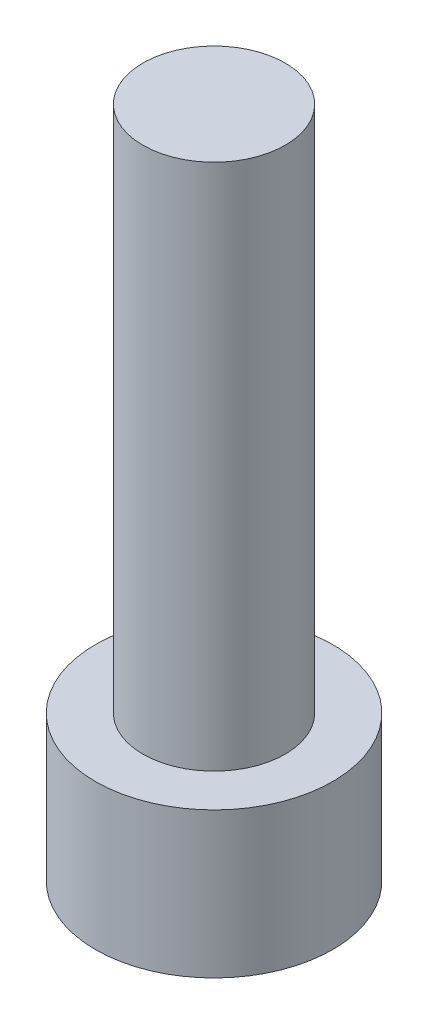
SolidWorks part; units mm, degrees
ref_plane "Front Plane" through (0, 0, 0) normal (0, 0, 1) x (1, 0, 0)
ref_plane "Top Plane" through (0, 0, 0) normal (0, 1, 0) x (1, 0, 0)
ref_plane "Right Plane" through (0, 0, 0) normal (1, 0, 0) x (0, 0, -1)
sketch "Sketch1" plane through (0, 0, 0) normal (0, 1, 0) x (1, 0, 0)
  circle A0 centre (0, 0) radius 2.8575
  dimension "D1" = 5.715
extrude "Boss-Extrude1" add sketch "Sketch1" along normal blind 3.5052
sketch "Sketch2" plane through (0, 0, 0) normal (0, -1, 0) x (1, 0, 0)
  line L1 (1.604, 0) -> (0.802, 1.3891)
  line L2 (0.802, 1.3891) -> (-0.802, 1.3891)
  line L3 (-0.802, 1.3891) -> (-1.604, 0)
  line L4 (-1.604, 0) -> (-0.802, -1.3891)
  line L5 (-0.802, -1.3891) -> (0.802, -1.3891)
  line L6 (0.802, -1.3891) -> (1.604, 0)
  circle A0 centre (0, 0) radius 1.3891 construction
  dimension "D1" = 2.7781
extrude "Cut-Extrude1" cut sketch "Sketch2" against normal blind 1.9558
sketch "Sketch3" plane through (0, 3.5052, 0) normal (0, 1, 0) x (1, 0, 0)
  circle A0 centre (0, 0) radius 1.7145
  dimension "D1" = 3.429
extrude "Boss-Extrude2" add sketch "Sketch3" along normal blind 12.7
